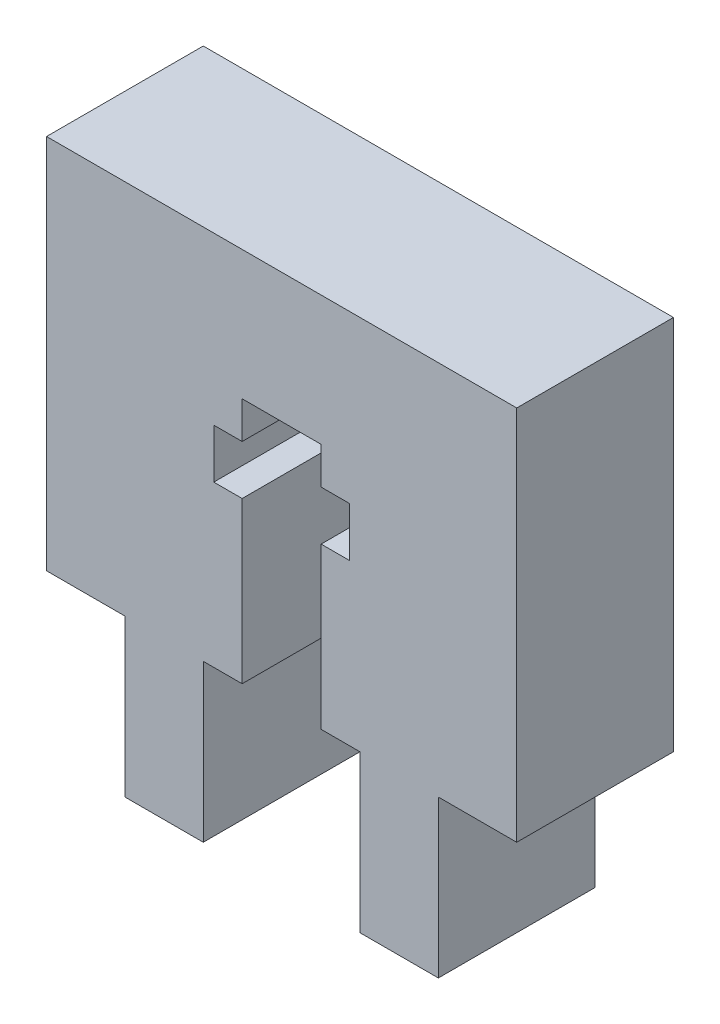
SolidWorks part; units mm, degrees
ref_plane "Front Plane" through (0, 0, 0) normal (0, 0, 1) x (1, 0, 0)
ref_plane "Top Plane" through (0, 0, 0) normal (0, 1, 0) x (1, 0, 0)
ref_plane "Right Plane" through (0, 0, 0) normal (1, 0, 0) x (0, 0, -1)
sketch "Sketch1" plane through (0, 0, 0) normal (0, 0, 1) x (1, 0, 0)
  line L0 (-3.175, 15.24) -> (15.875, 15.24)
  line L1 (3.175, 0) -> (9.525, 0)
  line L14 (0, 0) -> (0, -6.35)
  line L15 (0, -6.35) -> (3.175, -6.35)
  line L16 (3.175, 0) -> (3.175, -6.35)
  line L18 (12.7, 0) -> (12.7, -6.35)
  line L19 (12.7, -6.35) -> (9.525, -6.35)
  line L20 (9.525, 0) -> (9.525, -6.35)
  line L23 (0, 0) -> (-3.175, 0)
  line L24 (-3.175, 15.24) -> (-3.175, 0)
  line L27 (12.7, 0) -> (15.875, 0)
  line L28 (15.875, 15.24) -> (15.875, 0)
  dimension "D1" = 15.24
  dimension "D3" = 6.35
  dimension "D5" = 19.05
extrude "Boss-Extrude1" add sketch "Sketch1" along normal blind 6.35
sketch "Sketch3" plane through (0, 0, 6.35) normal (0, 0, 1) x (1, 0, 0)
  line L0 (3.175, 0) -> (9.525, 0) construction
  line L1 (4.75, 0) -> (7.95, 0)
  line L2 (4.75, 0) -> (4.75, 6.5)
  line L3 (4.75, 10) -> (7.95, 10)
  line L4 (7.95, 0) -> (7.95, 6.5)
  line L5 (6.35, 0) -> (6.35, 10) construction
  line L6 (4.75, 8.5) -> (3.6, 8.5)
  line L7 (7.95, 8.5) -> (7.95, 10)
  line L8 (4.75, 6.5) -> (3.6, 6.5)
  line L9 (3.6, 8.5) -> (3.6, 6.5)
  line L10 (7.95, 8.5) -> (9.1, 8.5)
  line L12 (7.95, 6.5) -> (9.1, 6.5)
  line L13 (9.1, 8.5) -> (9.1, 6.5)
  line L14 (3.6, 7.5) -> (9.1, 7.5) construction
  line L15 (4.75, 8.5) -> (4.75, 10)
  point P18 (6.35, 0)
  dimension "D1" = 10
  dimension "D2" = 7.5
  dimension "D3" = 2
  dimension "D4" = 5.5
  dimension "D5" = 3.2
extrude "Cut-Extrude3" cut sketch "Sketch3" against normal through all
